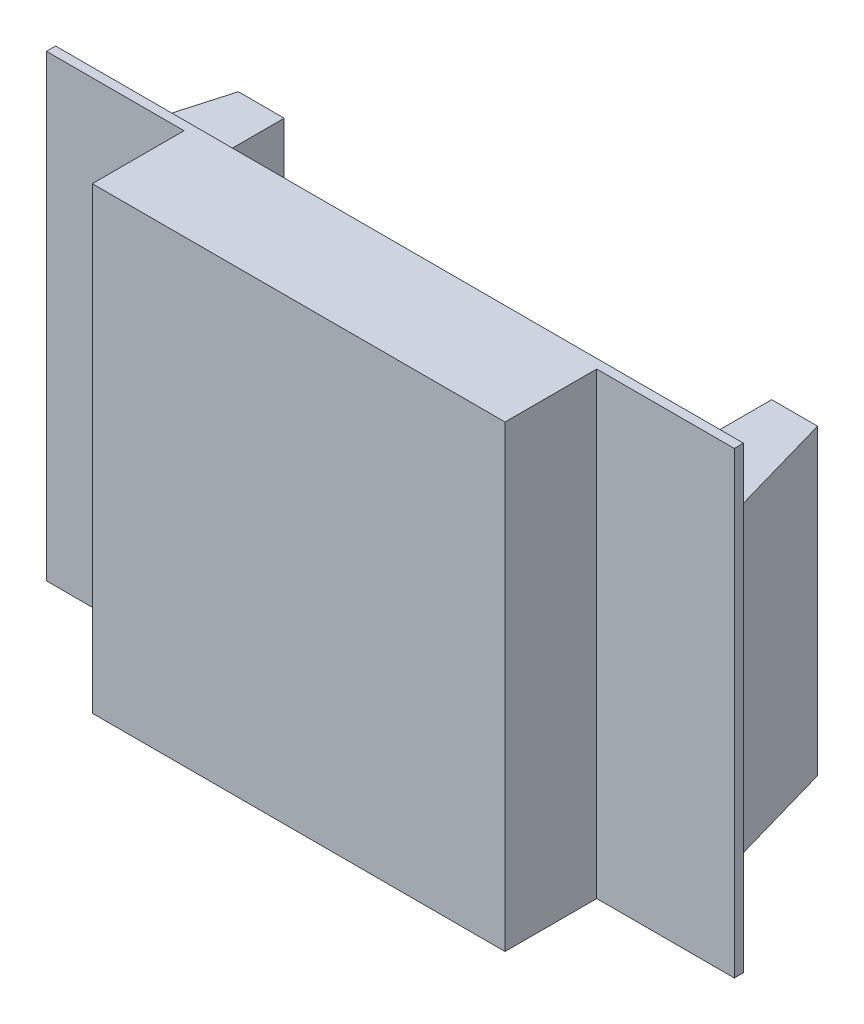
SolidWorks part; units mm, degrees
ref_plane "Front Plane" through (0, 0, 0) normal (0, 0, 1) x (1, 0, 0)
ref_plane "Top Plane" through (0, 0, 0) normal (0, 1, 0) x (1, 0, 0)
ref_plane "Right Plane" through (0, 0, 0) normal (1, 0, 0) x (0, 0, -1)
sketch "Sketch1" plane through (0, 0, 0) normal (0, 0, 1) x (1, 0, 0)
  line L1 (-42.4202, 41.3564) -> (32.5798, 41.3564)
  line L2 (-42.4202, 41.3564) -> (-42.4202, -8.6436)
  line L3 (-42.4202, -8.6436) -> (32.5798, -8.6436)
  line L4 (32.5798, 41.3564) -> (32.5798, -8.6436)
  dimension "D1" = 75
  dimension "D2" = 50
extrude "Boss-Extrude1" add sketch "Sketch1" along normal blind 1
sketch "Sketch2" plane through (0, 0, 0) normal (0, 1, 0) x (1, 0, 0)
  line L0 (32.5798, -1) -> (-42.4202, -1) construction
  line L1 (-27.4202, -1) -> (17.5798, -1)
  line L2 (-27.4202, -1) -> (-27.4202, -11)
  line L3 (-27.4202, -11) -> (17.5798, -11)
  line L4 (17.5798, -1) -> (17.5798, -11)
  line L5 (32.5798, -1) -> (32.5798, 0) construction
  dimension "D1" = 15
  dimension "D2" = 15
  dimension "D3" = 10
extrude "Boss-Extrude2" add sketch "Sketch2" along normal up to surface and the other way up to surface up to face at (-4.9202, 41.3564, 0.5) other way up to face at (-4.9202, -8.6436, 0.5)
sketch "Sketch4" plane through (0, 0, 0) normal (0, 1, 0) x (1, 0, 0)
  line L0 (-40.4965, 0) -> (-36.4965, 14)
  line L1 (32.5798, 0) -> (-42.4202, 0) construction
  line L2 (-36.4965, 14) -> (-31.4965, 14)
  line L3 (-31.4965, 14) -> (-31.4965, 0)
  line L4 (-31.4965, 0) -> (-40.4965, 0)
  line L5 (-4.9202, 0) -> (-4.9202, 27.7647) construction
  line L6 (21.6561, 0) -> (30.6561, 0)
  line L7 (21.6561, 14) -> (21.6561, 0)
  line L8 (30.6561, 0) -> (26.6561, 14)
  line L9 (26.6561, 14) -> (21.6561, 14)
  dimension "D1" = 14
  dimension "D2" = 9
  dimension "D3" = 4
extrude "Boss-Extrude5" add sketch "Sketch4" along normal blind 33
